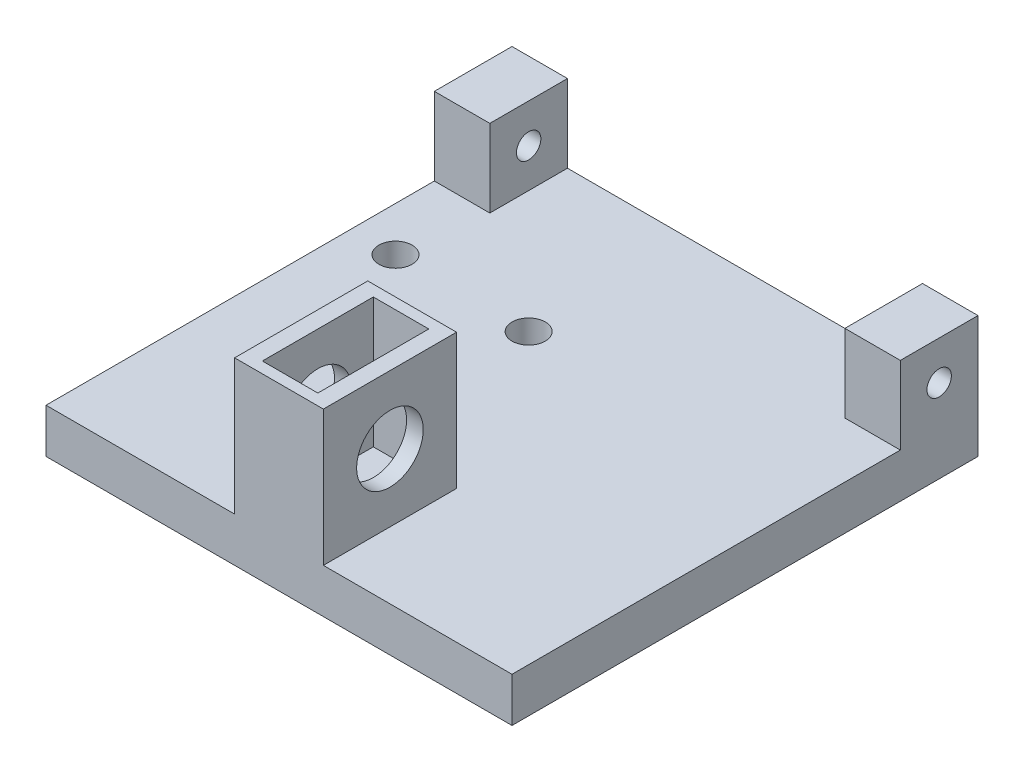
SolidWorks part; units mm, degrees
ref_plane "Front Plane" through (0, 0, 0) normal (0, 0, 1) x (1, 0, 0)
ref_plane "Top Plane" through (0, 0, 0) normal (0, 1, 0) x (1, 0, 0)
ref_plane "Right Plane" through (0, 0, 0) normal (1, 0, 0) x (0, 0, -1)
sketch "Sketch2" plane through (0, 0, 0) normal (0, 1, 0) x (1, 0, 0)
  line L1 (-40.4037, 21.6678) -> (1.5963, 21.6678)
  line L2 (-40.4037, 21.6678) -> (-40.4037, -20.3322)
  line L3 (-40.4037, -20.3322) -> (1.5963, -20.3322)
  line L4 (1.5963, 21.6678) -> (1.5963, -20.3322)
extrude "Boss-Extrude1" add sketch "Sketch2" along normal blind 4
sketch "Sketch4" plane through (0, 4, 0) normal (0, 1, 0) x (1, 0, 0)
  line L1 (-40.4037, 21.6678) -> (-35.4037, 21.6678)
  line L2 (-40.4037, 21.6678) -> (-40.4037, 14.6678)
  line L3 (-40.4037, 14.6678) -> (-35.4037, 14.6678)
  line L4 (-35.4037, 21.6678) -> (-35.4037, 14.6678)
  line L5 (1.5963, 21.6678) -> (-3.4037, 21.6678)
  line L6 (1.5963, 21.6678) -> (1.5963, 14.6678)
  line L7 (1.5963, 14.6678) -> (-3.4037, 14.6678)
  line L8 (-3.4037, 21.6678) -> (-3.4037, 14.6678)
extrude "Boss-Extrude2" add sketch "Sketch4" along normal blind 7
sketch "Sketch5" plane through (-35.4037, 0, 0) normal (1, 0, 0) x (0, 0, -1)
  circle A0 centre (18.1678, 7.5) radius 1.1
extrude "Cut-Extrude2" cut sketch "Sketch5" against normal blind 5
sketch "Sketch6" plane through (-3.4037, 0, 0) normal (-1, 0, 0) x (0, 0, 1)
  circle A0 centre (-18.1678, 7.5) radius 1.1
extrude "Cut-Extrude3" cut sketch "Sketch6" against normal blind 5
sketch "Sketch8" plane through (0, 0, 0) normal (0, -1, 0) x (1, 0, 0)
  circle A0 centre (-36.4037, -7.1678) radius 1.5
  circle A1 centre (-24.4037, -7.1678) radius 1.5
extrude "Cut-Extrude5" cut sketch "Sketch8" against normal blind 4
sketch "Sketch9" plane through (0, 4, 0) normal (0, 1, 0) x (1, 0, 0)
  line L1 (-40.4037, -20.3322) -> (1.5963, -20.3322) construction
  line L5 (-23.4037, -20.3322) -> (-15.4037, -20.3322)
  line L6 (-23.4037, -20.3322) -> (-23.4037, -8.3322)
  line L7 (-23.4037, -8.3322) -> (-15.4037, -8.3322)
  line L8 (-15.4037, -20.3322) -> (-15.4037, -8.3322)
extrude "Boss-Extrude3" add sketch "Sketch9" along normal blind 12.2
sketch "Sketch10" plane through (0, 16.2, 0) normal (0, 1, 0) x (1, 0, 0)
  line L10 (-21.9037, -9.3322) -> (-16.9037, -9.3322)
  line L11 (-21.9037, -9.3322) -> (-21.9037, -19.3322)
  line L12 (-21.9037, -19.3322) -> (-16.9037, -19.3322)
  line L13 (-16.9037, -9.3322) -> (-16.9037, -19.3322)
extrude "Cut-Extrude6" cut sketch "Sketch10" against normal blind 11.7
sketch "Sketch12" plane through (-15.4037, 0, 0) normal (1, 0, 0) x (0, 0, -1)
  circle A0 centre (-14.3322, 10.1) radius 3
extrude "Cut-Extrude7" cut sketch "Sketch12" against normal blind 8
